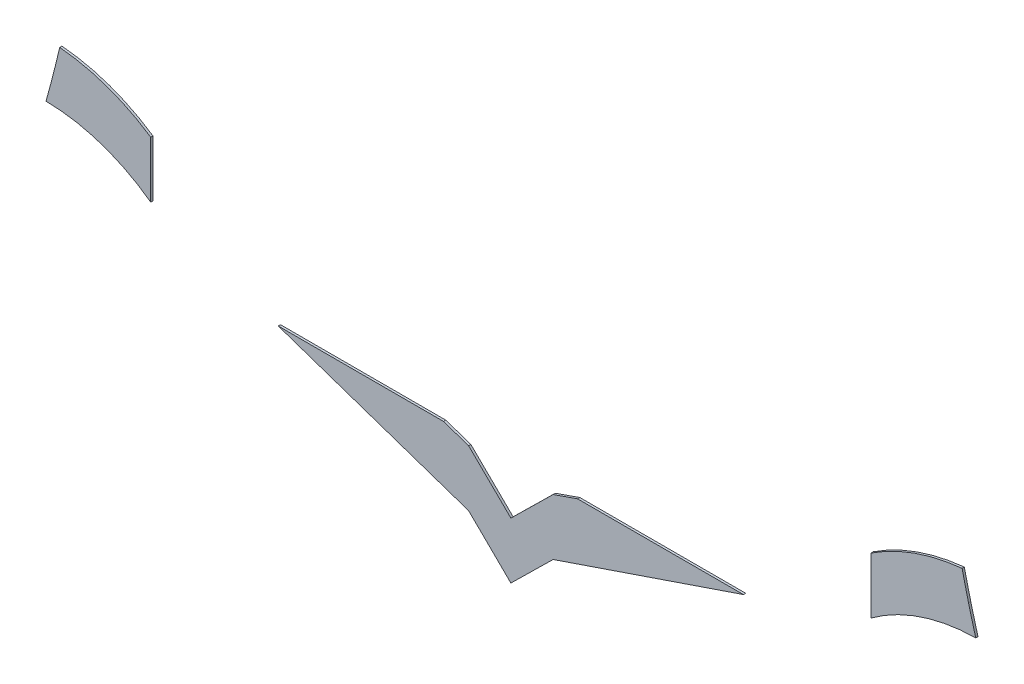
SolidWorks part; units mm, degrees
ref_plane "Alzado" through (0, 0, 0) normal (0, 0, 1) x (1, 0, 0)
ref_plane "Planta" through (0, 0, 0) normal (0, 1, 0) x (1, 0, 0)
ref_plane "Vista lateral" through (0, 0, 0) normal (1, 0, 0) x (0, 0, -1)
sketch "Model" plane through (0, 0, 0) normal (0, 0, 1) x (1, 0, 0)
  line L0 (20.9064, -14.7424) -> (20.9062, -12.2402)
  line L1 (33.9161, -16.6708) -> (26.5717, -16.6708)
  line L2 (52.9071, -12.2387) -> (52.9071, -14.7409)
  line L3 (39.8708, -16.6708) -> (38.7823, -17.0502)
  line L4 (38.7823, -17.0502) -> (36.9069, -18.8942)
  line L5 (36.9069, -18.8942) -> (35.0314, -17.0504)
  line L6 (35.0314, -17.0504) -> (33.9161, -16.6708)
  line L7 (47.2391, -16.6708) -> (38.7823, -19.5502)
  line L8 (38.7823, -19.5502) -> (36.9072, -21.3942)
  line L9 (26.5717, -16.6708) -> (35.0316, -19.5504)
  line L10 (35.0316, -19.5504) -> (36.9072, -21.3942)
  line L11 (47.2391, -16.6708) -> (39.8708, -16.6708)
  arc A0 (20.9062, -12.2402) -> (16.8627, -10.8061) centre (16.1203, -19.3165) ccw
  arc A1 (56.9529, -10.804) -> (52.9071, -12.2387) centre (57.8516, -19.7603) ccw
  arc A2 (57.5607, -13.1783) -> (52.9071, -14.7409) centre (57.6555, -21.1714) ccw
  arc A3 (20.9064, -14.7424) -> (16.2526, -13.1802) centre (16.1586, -21.1734) ccw
  arc A4 (56.9529, -10.804) -> (57.2393, -11.9857) centre (105.8389, 0.4174) ccw
  arc A5 (57.2393, -11.9857) -> (57.5596, -13.1783) centre (105.2556, 0.2733) ccw
  arc A6 (16.2537, -13.1802) -> (16.8627, -10.8061) centre (-32.4832, 0.5859) ccw
extrude "Saliente-Extruir1" add sketch "Model" along normal blind 0.1 contours A6 A3 L0 A0 | L7 L11 L3 L4 L5 L6 L1 L9 L10 L8 | A5 A4 A1 L2 A2
